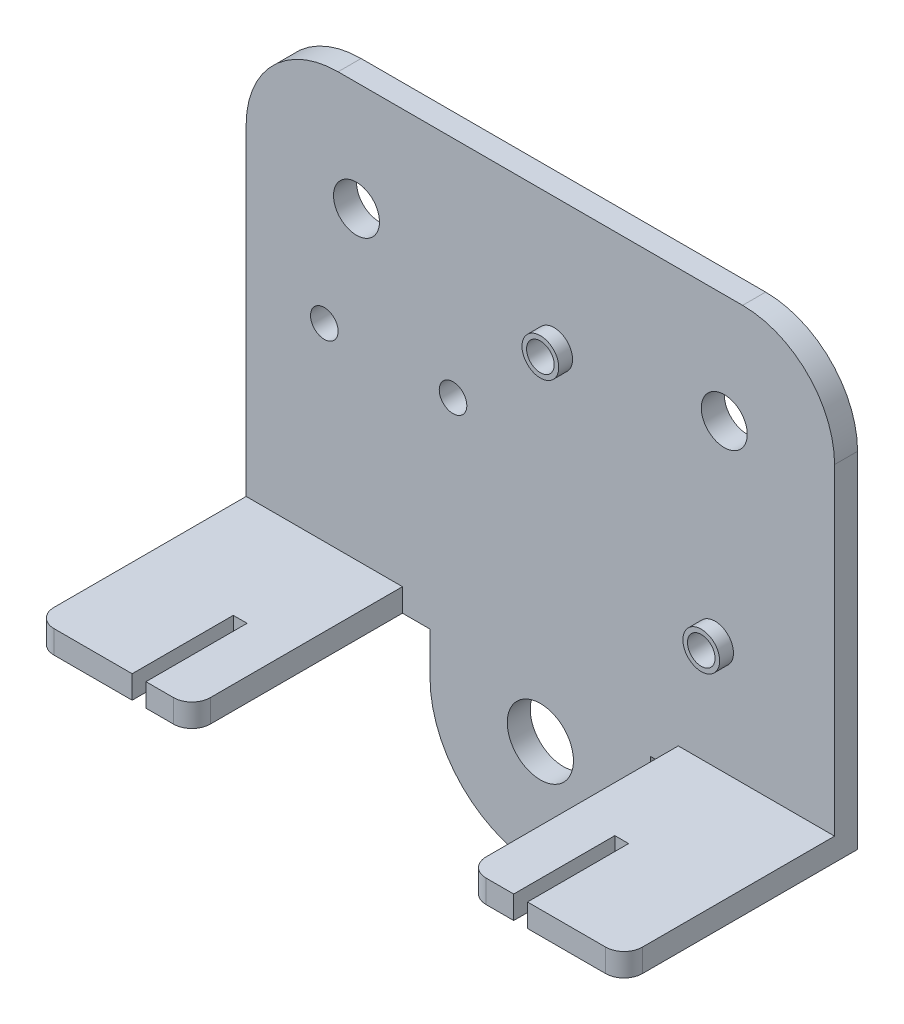
SolidWorks part; units mm, degrees
ref_plane "Front Plane" through (0, 0, 0) normal (0, 0, 1) x (1, 0, 0)
ref_plane "Top Plane" through (0, 0, 0) normal (0, 1, 0) x (1, 0, 0)
ref_plane "Right Plane" through (0, 0, 0) normal (1, 0, 0) x (0, 0, -1)
sketch "Sketch1" plane through (0, 0, 0) normal (0, 0, 1) x (1, 0, 0)
  line L0 (-12, -28.35) -> (-12, -23.75)
  line L1 (-32, 23.75) -> (32, 23.75)
  line L2 (-32, 23.75) -> (-32, -23.75)
  line L3 (-32, -23.75) -> (-12, -23.75)
  line L4 (32, 23.75) -> (32, -23.75)
  line L5 (-32, 23.75) -> (32, -23.75) construction
  line L6 (-32, -23.75) -> (32, 23.75) construction
  line L7 (12, -28.35) -> (12, -23.75)
  line L8 (12, -23.75) -> (32, -23.75)
  line L9 (0, -55) -> (0, 55) construction
  arc A0 (-12, -28.35) -> (12, -28.35) centre (0, -28.35) ccw
  circle A1 centre (0, -28.35) radius 3.6
  circle A2 centre (-20, 11.85) radius 2.5
  circle A3 centre (19, -9.5) radius 1.5
  circle A4 centre (1.5, 9.4) radius 1.5
  circle A5 centre (20, 11.85) radius 2.5
  circle A6 centre (-23.5, -0.7) radius 1.5
  circle A7 centre (-9.5, -0.7) radius 1.5
  point P0 (0, 0)
  dimension "D3" = 24
  dimension "D5" = 7.2
  dimension "D6" = 5
  dimension "D9" = 3
  dimension "D10" = 19
  dimension "D14" = 3
  dimension "D17" = 9.5
  dimension "D1" = 64
  dimension "D2" = 47.5
  dimension "D4" = 52.1
  dimension "D7" = 11.9
  dimension "D8" = 20
  dimension "D11" = 33.25
  dimension "D12" = 1.5
  dimension "D13" = 14.35
  dimension "D15" = 24.45
  dimension "D16" = 23.5
extrude "Boss-Extrude1" add sketch "Sketch1" along normal mid plane 2.5
sketch "Sketch2" plane through (0, 0, 1.25) normal (0, 0, 1) x (1, 0, 0)
  circle A0 centre (19, -9.5) radius 2
  circle A1 centre (1.5, 9.4) radius 2
  circle A2 centre (19, -9.5) radius 1.5 construction
  circle A3 centre (1.5, 9.4) radius 1.5 construction
  circle A4 centre (19, -9.5) radius 1.5
  circle A5 centre (1.5, 9.4) radius 1.5
  dimension "D1" = 4
extrude "Boss-Extrude2" add sketch "Sketch2" along normal blind 1.5
sketch "Sketch3" plane through (0, 0, -1.25) normal (0, 0, -1) x (-1, 0, 0)
  circle A0 centre (9.5, -0.7) radius 2.7
  circle A1 centre (23.5, -0.7) radius 2.7
  circle A2 centre (9.5, -0.7) radius 1.5 construction
  circle A3 centre (23.5, -0.7) radius 1.5 construction
  circle A4 centre (9.5, -0.7) radius 1.5
  circle A5 centre (23.5, -0.7) radius 1.5
  dimension "D1" = 5.4
extrude "Boss-Extrude3" add sketch "Sketch3" along normal blind 4.5
fillet "Fillet1" radius 10 2 edges at (-32, 23.75, 0) (32, 23.75, 0)
sketch "Sketch4" plane through (0, 0, 1.25) normal (0, 0, 1) x (1, 0, 0)
  line L1 (-32, -23.75) -> (-15, -23.75)
  line L2 (-32, -23.75) -> (-32, -21.25)
  line L3 (-32, -21.25) -> (-15, -21.25)
  line L4 (-15, -23.75) -> (-15, -21.25)
  line L5 (32, -23.75) -> (15, -23.75)
  line L6 (32, -23.75) -> (32, -21.25)
  line L7 (32, -21.25) -> (15, -21.25)
  line L8 (15, -23.75) -> (15, -21.25)
  dimension "D1" = 30
  dimension "D2" = 2.5
extrude "Boss-Extrude4" add sketch "Sketch4" along normal blind 22.9
sketch "Sketch5" plane through (0, -21.25, 0) normal (0, 1, 0) x (1, 0, 0)
  line L0 (-15, -24.15) -> (-32, -24.15) construction
  line L1 (-20, -24.15) -> (-21.5, -24.15)
  line L2 (-20, -24.15) -> (-20, -13.15)
  line L3 (-20, -13.15) -> (-21.5, -13.15)
  line L4 (-21.5, -24.15) -> (-21.5, -13.15)
  line L5 (22, -1.25) -> (-22, -1.25) construction
  line L6 (0, -16.445) -> (0, 16.445) construction
  line L7 (20, -13.15) -> (21.5, -13.15)
  line L8 (21.5, -24.15) -> (21.5, -13.15)
  line L9 (20, -24.15) -> (21.5, -24.15)
  line L10 (20, -24.15) -> (20, -13.15)
  dimension "D1" = 1.5
  dimension "D2" = 11.9
  dimension "D3" = 40
extrude "Cut-Extrude1" cut sketch "Sketch5" against normal through all
fillet "Fillet2" radius 2 4 edges at (32, -22.5, 24.15) (15, -22.5, 24.15) (-15, -22.5, 24.15) (-32, -22.5, 24.15)
